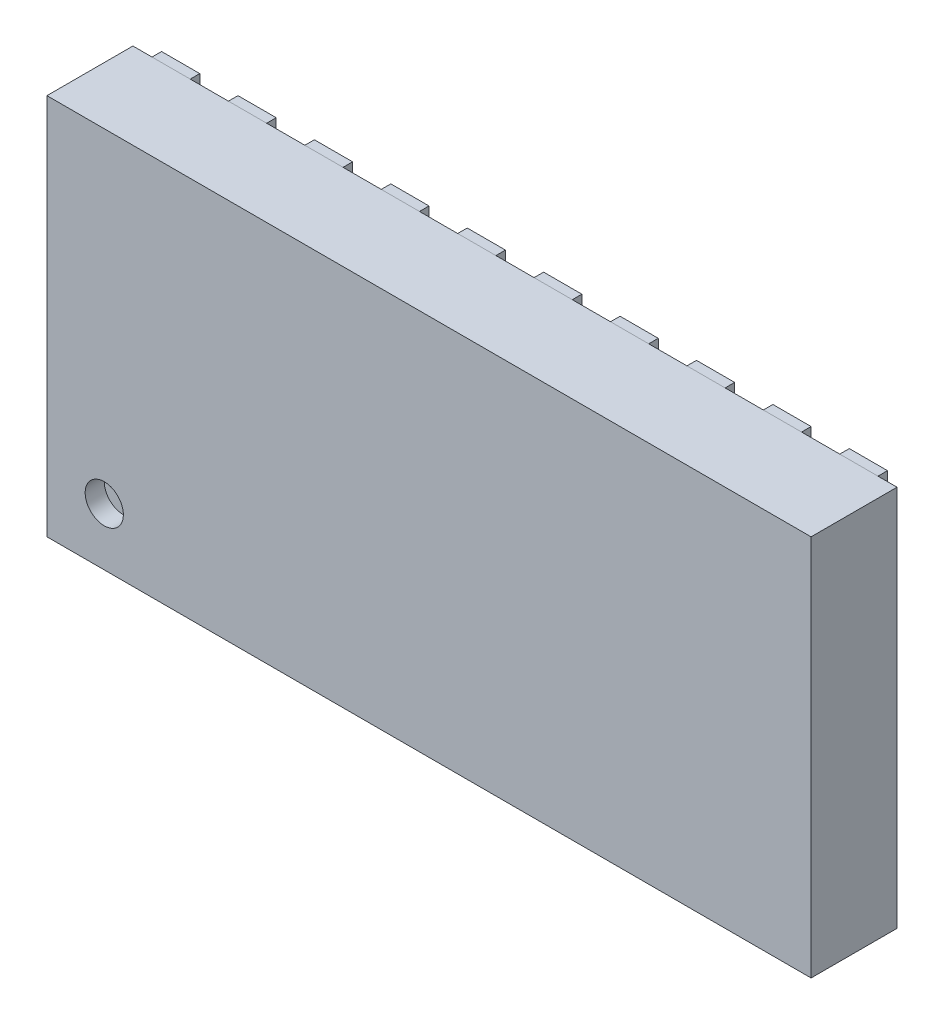
SolidWorks part; units mm, degrees
ref_plane "Front Plane" through (0, 0, 0) normal (0, 0, 1) x (1, 0, 0)
ref_plane "Top Plane" through (0, 0, 0) normal (0, 1, 0) x (1, 0, 0)
ref_plane "Right Plane" through (0, 0, 0) normal (1, 0, 0) x (0, 0, -1)
sketch "Sketch1" plane through (0, 0, 0) normal (0, 0, 1) x (1, 0, 0)
  line L1 (0, 0) -> (4, 0)
  line L2 (0, 0) -> (0, 2)
  line L3 (0, 2) -> (4, 2)
  line L4 (4, 0) -> (4, 2)
  dimension "D1" = 4
  dimension "D2" = 2
extrude "Boss-Extrude1" add sketch "Sketch1" along normal blind 0.45
sketch "Sketch2" plane through (0, 0, 0) normal (0, 0, -1) x (-1, 0, 0)
  line L0 (-2, 2) -> (-2, 0) construction
  line L1 (-4, 2) -> (0, 2) construction
  line L2 (0, 0) -> (-4, 0) construction
  line L3 (-3.8, 2) -> (-3.8, 1.45) construction
  line L4 (-4, 0) -> (-4, 2) construction
  line L5 (-4, 1) -> (0, 1) construction
  line L6 (0, 2) -> (0, 0) construction
  line L7 (-3.9, 2) -> (-3.7, 2)
  line L8 (-3.9, 2) -> (-3.9, 1.45)
  line L9 (-3.9, 1.45) -> (-3.7, 1.45)
  line L10 (-3.7, 2) -> (-3.7, 1.45)
  line L11 (-3.5, 2) -> (-3.3, 2)
  line L12 (-3.5, 2) -> (-3.5, 1.45)
  line L13 (-3.5, 1.45) -> (-3.3, 1.45)
  line L14 (-3.3, 2) -> (-3.3, 1.45)
  line L15 (-3.1, 2) -> (-2.9, 2)
  line L16 (-3.1, 2) -> (-3.1, 1.45)
  line L17 (-3.1, 1.45) -> (-2.9, 1.45)
  line L18 (-2.9, 2) -> (-2.9, 1.45)
  line L19 (-2.7, 2) -> (-2.5, 2)
  line L20 (-2.7, 2) -> (-2.7, 1.45)
  line L21 (-2.7, 1.45) -> (-2.5, 1.45)
  line L22 (-2.5, 2) -> (-2.5, 1.45)
  line L23 (-2.3, 2) -> (-2.1, 2)
  line L24 (-2.3, 2) -> (-2.3, 1.45)
  line L25 (-2.3, 1.45) -> (-2.1, 1.45)
  line L26 (-2.1, 2) -> (-2.1, 1.45)
  line L27 (-1.9, 2) -> (-1.7, 2)
  line L28 (-1.9, 2) -> (-1.9, 1.45)
  line L29 (-1.9, 1.45) -> (-1.7, 1.45)
  line L30 (-1.7, 2) -> (-1.7, 1.45)
  line L31 (-1.5, 2) -> (-1.3, 2)
  line L32 (-1.5, 2) -> (-1.5, 1.45)
  line L33 (-1.5, 1.45) -> (-1.3, 1.45)
  line L34 (-1.3, 2) -> (-1.3, 1.45)
  line L35 (-1.1, 2) -> (-0.9, 2)
  line L36 (-1.1, 2) -> (-1.1, 1.45)
  line L37 (-1.1, 1.45) -> (-0.9, 1.45)
  line L38 (-0.9, 2) -> (-0.9, 1.45)
  line L39 (-0.7, 2) -> (-0.5, 2)
  line L40 (-0.7, 2) -> (-0.7, 1.45)
  line L41 (-0.7, 1.45) -> (-0.5, 1.45)
  line L42 (-0.5, 2) -> (-0.5, 1.45)
  line L43 (-0.3, 2) -> (-0.1, 2)
  line L44 (-0.3, 2) -> (-0.3, 1.45)
  line L45 (-0.3, 1.45) -> (-0.1, 1.45)
  line L46 (-0.1, 2) -> (-0.1, 1.45)
  line L47 (-0.3, 0) -> (-0.3, 0.65)
  line L48 (-0.2, 2) -> (-0.2, 0) construction
  line L49 (-0.3, 0.65) -> (-0.1707, 0.65)
  line L50 (-0.3, 0) -> (-0.1, 0)
  line L51 (-0.5, 0) -> (-0.5, 0.55)
  line L52 (-0.7, 0.55) -> (-0.5, 0.55)
  line L53 (-0.7, 0) -> (-0.7, 0.55)
  line L54 (-0.7, 0) -> (-0.5, 0)
  line L55 (-0.9, 0) -> (-0.9, 0.55)
  line L56 (-1.1, 0.55) -> (-0.9, 0.55)
  line L57 (-1.1, 0) -> (-1.1, 0.55)
  line L58 (-1.1, 0) -> (-0.9, 0)
  line L59 (-1.3, 0) -> (-1.3, 0.55)
  line L60 (-1.5, 0.55) -> (-1.3, 0.55)
  line L61 (-1.5, 0) -> (-1.5, 0.55)
  line L62 (-1.5, 0) -> (-1.3, 0)
  line L63 (-1.7, 0) -> (-1.7, 0.55)
  line L64 (-1.9, 0.55) -> (-1.7, 0.55)
  line L65 (-1.9, 0) -> (-1.9, 0.55)
  line L66 (-1.9, 0) -> (-1.7, 0)
  line L67 (-2.1, 0) -> (-2.1, 0.55)
  line L68 (-2.3, 0.55) -> (-2.1, 0.55)
  line L69 (-2.3, 0) -> (-2.3, 0.55)
  line L70 (-2.3, 0) -> (-2.1, 0)
  line L71 (-2.5, 0) -> (-2.5, 0.55)
  line L72 (-2.7, 0.55) -> (-2.5, 0.55)
  line L73 (-2.7, 0) -> (-2.7, 0.55)
  line L74 (-2.7, 0) -> (-2.5, 0)
  line L75 (-2.9, 0) -> (-2.9, 0.55)
  line L76 (-3.1, 0.55) -> (-2.9, 0.55)
  line L77 (-3.1, 0) -> (-3.1, 0.55)
  line L78 (-3.1, 0) -> (-2.9, 0)
  line L79 (-3.3, 0) -> (-3.3, 0.55)
  line L80 (-3.5, 0.55) -> (-3.3, 0.55)
  line L81 (-3.5, 0) -> (-3.5, 0.55)
  line L82 (-3.5, 0) -> (-3.3, 0)
  line L83 (-3.7, 0) -> (-3.7, 0.55)
  line L84 (-3.9, 0.55) -> (-3.7, 0.55)
  line L85 (-3.9, 0) -> (-3.9, 0.55)
  line L86 (-3.9, 0) -> (-3.7, 0)
  line L87 (-0.1, 0.5793) -> (-0.1, 0)
  line L88 (-0.1707, 0.65) -> (-0.1, 0.5793)
  dimension "D1" = 0.2
  dimension "D2" = 0.55
  dimension "D3" = 1.8
  dimension "D5" = 3.6
  dimension "D6" = 0.55
  dimension "D7" = 0.65
  dimension "D8" = 45
  dimension "D9" = 0.1
  dimension "D4" = 10
extrude "Boss-Extrude2" add sketch "Sketch2" along normal blind 0.05 separate body
sketch "Sketch3" plane through (0, 0, 0.45) normal (0, 0, 1) x (1, 0, 0)
  line L0 (0, 2) -> (0, 0) construction
  line L3 (0, 0) -> (4, 0) construction
  circle A0 centre (0.3, 0.3) radius 0.1
  point P8 (0.1303, 0)
  dimension "D1" = 0.2
  dimension "D2" = 0.3
  dimension "D3" = 0.3
extrude "Cut-Extrude1" cut sketch "Sketch3" against normal blind 0.1
